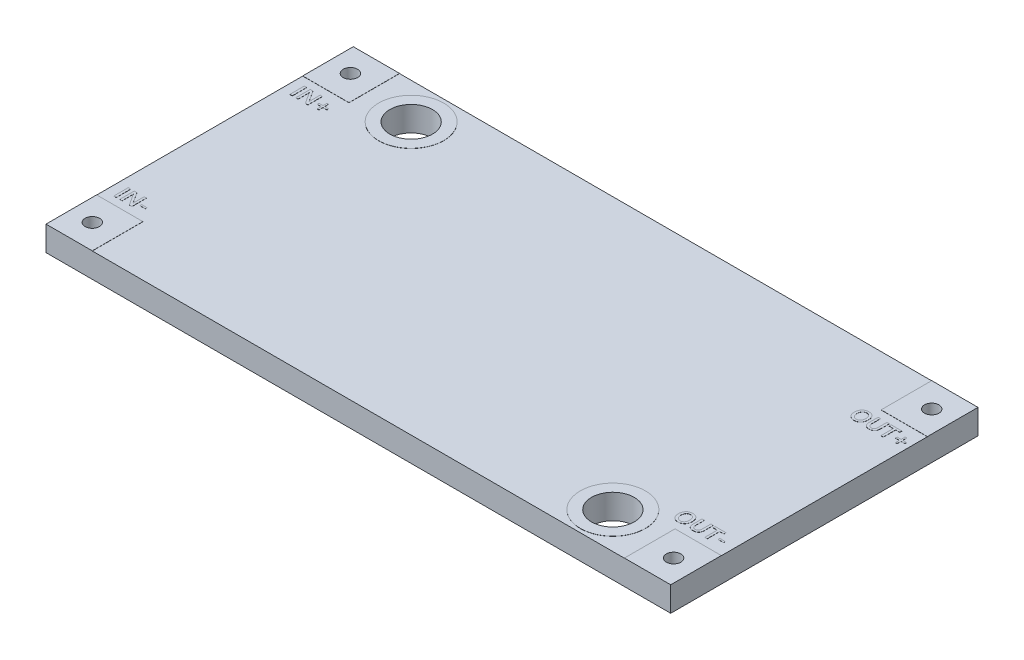
SolidWorks part; units mm, degrees
ref_plane "Front Plane" through (0, 0, 0) normal (0, 0, 1) x (1, 0, 0)
ref_plane "Top Plane" through (0, 0, 0) normal (0, 1, 0) x (1, 0, 0)
ref_plane "Right Plane" through (0, 0, 0) normal (1, 0, 0) x (0, 0, -1)
sketch "Sketch1" plane through (0, 0, 0) normal (0, 1, 0) x (1, 0, 0)
  line L1 (-21.6, -10.625) -> (21.6, -10.625)
  line L2 (-21.6, -10.625) -> (-21.6, 10.625)
  line L3 (-21.6, 10.625) -> (21.6, 10.625)
  line L4 (21.6, -10.625) -> (21.6, 10.625)
  line L5 (-21.6, -10.625) -> (21.6, 10.625) construction
  line L6 (-21.6, 10.625) -> (21.6, -10.625) construction
  point P0 (0, 0)
  dimension "D1" = 43.2
  dimension "D2" = 21.25
extrude "Boss-Extrude1" add sketch "Sketch1" along normal blind 1.7
sketch "Sketch2" plane through (0, 0, 0) normal (0, 1, 0) x (1, 0, 0)
  line L0 (21.6, 10.625) -> (-21.6, 10.625) construction
  line L1 (-21.6, 10.625) -> (-21.6, -10.625) construction
  line L2 (0, 0) -> (-4.0625, 0) construction
  circle A0 centre (-15.1, 8.125) radius 1.475
  circle A1 centre (-20.1, 8.925) radius 0.5
  circle A2 centre (15.1, -8.125) radius 1.475
  circle A3 centre (20.1, -8.925) radius 0.5
  circle A4 centre (20.1, 8.925) radius 0.5
  circle A5 centre (-20.1, -8.925) radius 0.5
  point P14 (0, 0)
  dimension "D1" = 1
  dimension "D4" = 2.95
  dimension "D2" = 1.7
  dimension "D3" = 1.5
  dimension "D5" = 2.5
  dimension "D6" = 6.5
  dimension "D7" = 2
extrude "Cut-Extrude1" cut sketch "Sketch2" along normal through all
sketch "Sketch3" plane through (0, 1.7, 0) normal (0, 1, 0) x (1, 0, 0)
  line L0 (0, 0) -> (-4.2252, 0) construction
  line L1 (-21.6, 10.625) -> (-18.4, 10.625)
  line L2 (-21.6, 10.625) -> (-21.6, 7.125)
  line L3 (-21.6, 7.125) -> (-18.4, 7.125)
  line L4 (-18.4, 10.625) -> (-18.4, 7.125)
  line L5 (-18.4, -10.625) -> (-18.4, -7.125)
  line L6 (-21.6, -7.125) -> (-18.4, -7.125)
  line L7 (-21.6, -10.625) -> (-21.6, -7.125)
  line L8 (-21.6, -10.625) -> (-18.4, -10.625)
  line L9 (0, 0) -> (0, 4.7938) construction
  line L10 (21.6, -10.625) -> (18.4, -10.625)
  line L11 (21.6, -10.625) -> (21.6, -7.125)
  line L12 (21.6, -7.125) -> (18.4, -7.125)
  line L13 (18.4, -10.625) -> (18.4, -7.125)
  line L14 (18.4, 10.625) -> (18.4, 7.125)
  line L15 (21.6, 7.125) -> (18.4, 7.125)
  line L16 (21.6, 10.625) -> (21.6, 7.125)
  line L17 (21.6, 10.625) -> (18.4, 10.625)
  circle A0 centre (-15.1, 8.125) radius 2.25
  circle A1 centre (-15.1, 8.125) radius 1.475 construction
  circle A2 centre (-15.1, 8.125) radius 1.475
  circle A3 centre (15.1, -8.125) radius 2.25
  circle A4 centre (15.1, -8.125) radius 1.475 construction
  circle A5 centre (15.1, -8.125) radius 1.475
  circle A6 centre (-20.1, 8.925) radius 0.5 construction
  circle A7 centre (-20.1, 8.925) radius 0.5
  circle A8 centre (-20.1, -8.925) radius 0.5 construction
  circle A9 centre (-20.1, -8.925) radius 0.5
  circle A10 centre (20.1, 8.925) radius 0.5 construction
  circle A11 centre (20.1, 8.925) radius 0.5
  circle A12 centre (20.1, -8.925) radius 0.5 construction
  circle A13 centre (20.1, -8.925) radius 0.5
  dimension "D3" = 4.5
  dimension "D4" = 4.5
  dimension "D1" = 3.5
  dimension "D2" = 3.2
extrude "Boss-Extrude2" add sketch "Sketch3" along normal blind 0.01
sketch "Sketch4" plane through (0, 1.7, 0) normal (0, 1, 0) x (1, 0, 0)
  text T0 "<b>IN+</b>" font "Yu Gothic UI" height 1
  text T1 "<b>IN-</b>" font "Yu Gothic UI" height 1
  text T2 "<b>OUT+</b>" font "Yu Gothic UI" height 1
  text T3 "<b>OUT-</b>" font "Yu Gothic UI" height 1
extrude "Boss-Extrude3" add sketch "Sketch4" along normal blind 0.01
